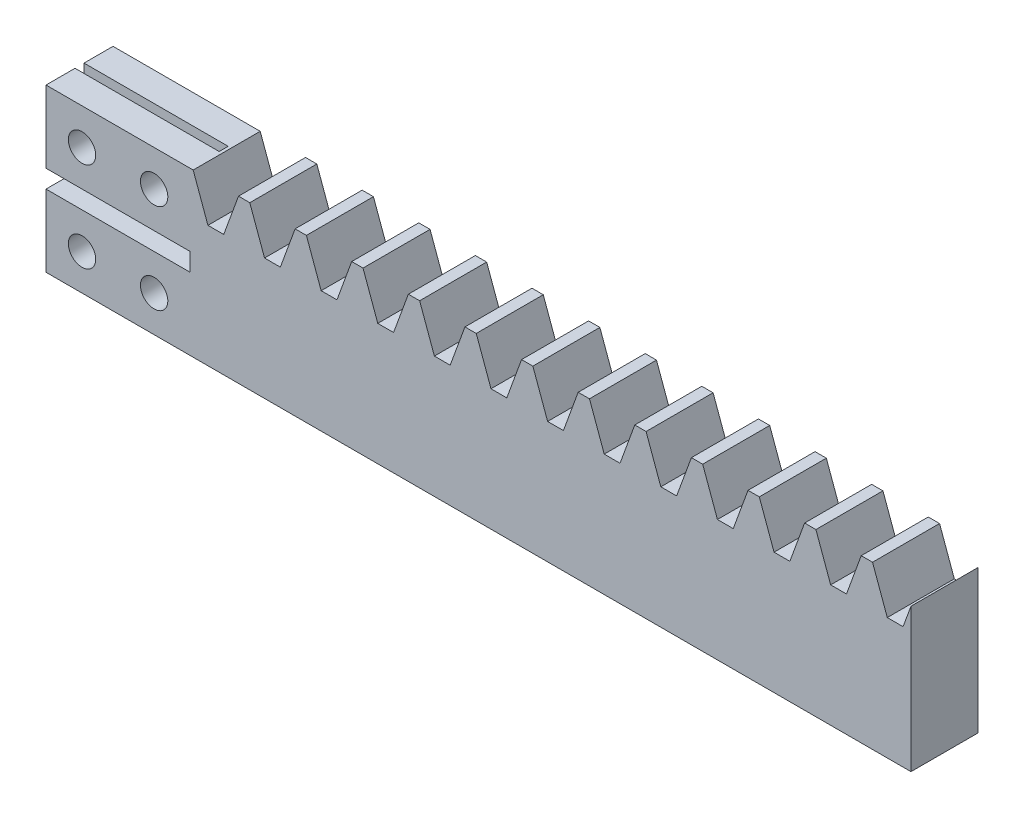
SolidWorks part; units mm, degrees
ref_plane "Plane1" through (0, 0, 0) normal (0, 0, 1) x (1, 0, 0)
ref_plane "Plane2" through (0, 0, 0) normal (0, 1, 0) x (1, 0, 0)
ref_plane "Plane3" through (0, 0, 0) normal (1, 0, 0) x (0, 0, -1)
sketch "HoldingSke" plane through (0, 0, 0) normal (0, 1, 0) x (1, 0, 0)
  line L0 (0, 0) -> (155.6602, -130.6144)
  line L1 (-15, 0) -> (100, 0) construction
  line L2 (0, 0) -> (-2.1039, 2.3779)
  line L3 (0, 0) -> (-11.863, 4.5341)
  line L4 (0, 0) -> (8.2587, 2.5249)
  line L5 (0, 0) -> (-23.7986, -8.8762)
  line L6 (0, 0) -> (-10.5278, -7.1032)
  line L9 (-71.009, 38.7566) -> (72.2002, 90.8805)
  line L10 (-76.2, 71.12) -> (-50.8, 71.12)
  line L11 (0, 0) -> (-11.811, 0)
  line L12 (-76.2, 101.6) -> (-76.0857, 101.6)
  line L13 (24.9733, 27.94) -> (52.9518, 28.4284)
  line L14 (24.9733, 27.94) -> (24.9746, 27.94)
  line L15 (24.9733, 27.94) -> (100.4006, 29.5858)
  circle A0 centre (0, 0) radius 19.05
  circle A1 centre (0, 0) radius 12.7
  circle A2 centre (0, 0) radius 12.7
  dimension "MPH" = 25.4
  dimension "Diameter" = 38.1
  dimension "Num_teeth" = 17
  dimension "Pitch" = 203.2
  dimension "Width" = 11.811
  dimension "Show_teeth" = 400
  dimension "Thickness" = 12.7
  dimension "Ap" = 20
  dimension "Pitch_height" = 25.4
  dimension "Backlash" = 0.1143
  dimension "Addendum_fac" = 1
  dimension "Dedendum_fac" = 1.25
  dimension "Clearance_fac" = 0.25
  dimension "Dedendum_add" = 0.0013
  dimension "Length" = 152.4
sketch "BlankSke" plane through (0, 0, 0) normal (0, 0, 1) x (1, 0, 0)
  line L1 (0, 0) -> (152.4, 0)
  line L2 (0, 0) -> (0, 28.575)
  line L3 (0, 28.575) -> (152.4, 28.575)
  line L4 (152.4, 0) -> (152.4, 28.575)
  dimension "Length" = 152.4
  dimension "Blank_height" = 28.575
extrude "Blank" add sketch "BlankSke" against normal blind 11.811
sketch "TooCutSkeIll" plane through (0, 0, 0) normal (0, 0, 1) x (1, 0, 0)
  line L0 (-3.9617, 28.4914) -> (-1.5824, 21.9544)
  line L1 (-0.8354, 21.4312) -> (0.8354, 21.4312)
  line L2 (1.5824, 21.9544) -> (3.9617, 28.4914)
  line L3 (152.4, 28.575) -> (0, 28.575) construction
  line L4 (0, 0) -> (0, 64.897) construction
  line L5 (-13.208, 25.4) -> (12.954, 25.4) construction
  line L6 (0, 0) -> (152.4, 0) construction
  line L7 (2.8365, 25.4) -> (2.8365, 48.7463) construction
  line L8 (-2.8365, 25.4) -> (-2.8365, 48.7463) construction
  line L9 (4.0811, 28.575) -> (4.0811, 28.6004)
  line L10 (-4.0811, 28.575) -> (-4.0811, 28.6004)
  line L11 (-4.0811, 28.6004) -> (4.0811, 28.6004)
  arc A0 (0.8354, 21.4312) -> (1.5824, 21.9544) centre (0.8354, 22.2263) ccw
  arc A1 (-1.5824, 21.9544) -> (-0.8354, 21.4312) centre (-0.8354, 22.2263) ccw
  arc A2 (4.0811, 28.575) -> (3.9617, 28.4914) centre (4.0811, 28.448) ccw
  arc A3 (-3.9617, 28.4914) -> (-4.0811, 28.575) centre (-4.0811, 28.448) ccw
  dimension "Root_fillet" = 0.795
  dimension "Break_rad" = 0.127
  dimension "Pitch_height" = 25.4
  dimension "Gap_width" = 5.6731
  dimension "Dedendum" = 3.9688
  dimension "Addendum_plus" = 3.2004
  dimension "Pressure_angle" = 20
extrude "ToothCutIll" [suppressed] cut sketch "TooCutSkeIll" against normal through all
sketch "TooCutSkeSim" plane through (0, 0, 0) normal (0, 0, 1) x (1, 0, 0)
  line L0 (1.392, 21.4312) -> (-1.392, 21.4312)
  line L1 (4.0014, 28.6004) -> (1.392, 21.4312)
  line L2 (0, 17.4625) -> (0, 53.467) construction
  line L3 (4.0014, 28.6004) -> (-4.0014, 28.6004)
  line L6 (-4.0014, 28.6004) -> (-1.392, 21.4312)
  line L9 (-2.8365, 25.4) -> (2.8365, 25.4) construction
  line L10 (0, 0) -> (152.4, 0) construction
  line L11 (2.8365, 25.4) -> (2.8365, 53.467) construction
  line L12 (-2.8365, 25.4) -> (-2.8365, 53.467) construction
  dimension "Pitch_height" = 25.4
  dimension "Pressure_angle" = 20
  dimension "Gap_width" = 5.6731
  dimension "Dedendum" = 3.9688
  dimension "Addendum_plus" = 3.2004
extrude "ToothCutSim" cut sketch "TooCutSkeSim" against normal through all
pattern_linear "TeethCuts" count 16 spacing 9.9746 along (1, 0, 0) of "ToothCutIll", "ToothCutSim"
sketch "Sketch2" plane through (0, 0, 0) normal (0, 0, 1) x (1, 0, 0)
  line L1 (0, 0) -> (23.9413, 0)
  line L2 (0, 0) -> (0, 28.575)
  line L3 (0, 28.575) -> (23.9413, 28.575)
  line L4 (23.9413, 0) -> (23.9413, 28.575)
extrude "Boss-Extrude1" add sketch "Sketch2" against normal blind 11.811
sketch "Sketch3" plane through (0, 0, 0) normal (0, 0, 1) x (1, 0, 0)
  line L0 (0, 12.7) -> (25.4, 12.7)
  line L1 (0, 28.575) -> (0, 0) construction
  line L2 (25.4, 12.7) -> (25.4, 15.875)
  line L3 (25.4, 15.875) -> (0, 15.875)
  line L4 (0, 14.2875) -> (13.4363, 14.2875) construction
  dimension "D1" = 25.4
  dimension "D2" = 3.175
  dimension "D3" = 3.175
extrude "Cut-Extrude1" cut sketch "Sketch3" against normal through all and the other way through all
sketch "Sketch4" plane through (0, 28.575, 0) normal (0, 1, 0) x (1, 0, 0)
  line L0 (0, 6.6993) -> (25.4, 6.6993)
  line L1 (0, 11.811) -> (0, 0) construction
  line L2 (25.4, 6.6993) -> (25.4, 5.1118)
  line L3 (25.4, 5.1118) -> (0, 5.1117)
  line L4 (0, 5.9055) -> (23.2466, 5.9055) construction
  dimension "D1" = 0.7937
  dimension "D2" = 0.7937
  dimension "D3" = 25.4
extrude "Cut-Extrude5" cut sketch "Sketch4" against normal through all and the other way through all flip side to cut
sketch "Sketch5" plane through (0, 0, 0) normal (0, 0, 1) x (1, 0, 0)
  line L0 (0, 28.575) -> (0, 15.875) construction
  line L1 (25.4, 15.875) -> (0, 15.875) construction
  line L2 (0, 12.7) -> (25.4, 12.7) construction
  circle A0 centre (6.35, 22.225) radius 2.413
  circle A1 centre (19.05, 22.225) radius 2.413
  circle A2 centre (19.05, 6.35) radius 2.413
  circle A3 centre (6.35, 6.35) radius 2.413
  dimension "D1" = 4.826
  dimension "D2" = 12.7
  dimension "D3" = 6.35
  dimension "D4" = 6.35
  dimension "D5" = 6.35
extrude "Cut-Extrude6" cut sketch "Sketch5" against normal blind 12.446
equation "' \"Pitch@HoldingSke\" = 4"
equation "' \"Num_teeth@HoldingSke\" = 12"
equation "' \"Ap@HoldingSke\" =  20"
equation "' \"Width@HoldingSke\" = 0.25"
equation "' \"Show_teeth@HoldingSke\" = 500"
equation "' \"Backlash@HoldingSke\" = 0.009"
equation "' \"Addendum_fac@HoldingSke\" = 1.0"
equation "' \"Dedendum_fac@HoldingSke\" = 1.25"
equation "' \"Dedendum_add@HoldingSke\" = 0.00005"
equation "' \"Clearance_fac@HoldingSke\" = 0.25"
equation "' \"Pitch_height@HoldingSke\" = 1"
equation "' \"Length@HoldingSke\" = 4.71"
equation "\"MPH@HoldingSke\" = \"Dedendum_fac@HoldingSke\" / \"Pitch@HoldingSke\" + 2 * \"Dedendum_add@HoldingSke\" + 0.002"
equation "\"MPH@HoldingSke\" = ((sgn( \"MPH@HoldingSke\" - \"Pitch_height@HoldingSke\")+1)*( \"MPH@HoldingSke\" - \"Pitch_height@HoldingSke\"))/2 + \"Pitch_height@HoldingSke\""
equation "\"Blank_height@BlankSke\" = \"Pitch_height@HoldingSke\" + \"Addendum_fac@HoldingSke\"  / \"Pitch@HoldingSke\" "
equation "\"Length@BlankSke\" =  \"Length@HoldingSke\""
equation "\"Face_width@Blank\" = \"Width@HoldingSke\""
equation "\"Pressure_angle@TooCutSkeIll\" = \"Ap@HoldingSke\""
equation "\"Addendum_plus@TooCutSkeIll\" =  \"Addendum_fac@HoldingSke\"  / \"Pitch@HoldingSke\" + 0.001"
equation "\"Dedendum@TooCutSkeIll\" = \"Dedendum_fac@HoldingSke\"  / \"Pitch@HoldingSke\""
equation "\"Pitch_height@TooCutSkeIll\" =  \"MPH@HoldingSke\""
equation "\"Gap_width@TooCutSkeIll\" = 3.14159265 / 2 / \"Pitch@HoldingSke\" + 6 * \"Backlash@HoldingSke\""
equation "\"Pressure_angle@TooCutSkeSim\" = \"Ap@HoldingSke\""
equation "\"Addendum_plus@TooCutSkeSim\" =  \"Addendum_fac@HoldingSke\"  / \"Pitch@HoldingSke\" + 0.001"
equation "\"Dedendum@TooCutSkeSim\" = \"Dedendum_fac@HoldingSke\"  / \"Pitch@HoldingSke\""
equation "\"Pitch_height@TooCutSkeSim\" =  \"MPH@HoldingSke\""
equation "\"Gap_width@TooCutSkeSim\" = 3.14159265 / 2 / \"Pitch@HoldingSke\" + 6 * \"Backlash@HoldingSke\""
equation "\"Root_fillet@TooCutSkeIll\" = \"Clearance_fac@HoldingSke\" / \"Pitch@HoldingSke\" + \"Dedendum_add@HoldingSke\""
equation "\"Break_rad@TooCutSkeIll\" = 0.02 / \"Pitch@HoldingSke\" * 2"
equation "\"Linear_pitch@TeethCuts\" = 3.14159265 / \"Pitch@HoldingSke\""
equation "\"Num_teeth@HoldingSke\" = int( ( \"Length@HoldingSke\" + 0 ) / (3.14159265 / \"Pitch@HoldingSke\")) + 0.9999  + 1"
equation " \"Num_teeth@TeethCuts\" = int( \"Show_teeth@HoldingSke\" ) + 1"
equation " \"Num_teeth@TeethCuts\" = ((sgn( \"Num_teeth@TeethCuts\" - \"Num_teeth@HoldingSke\" )-1)*( \"Num_teeth@TeethCuts\" - \"Num_teeth@HoldingSke\" ))/-2+ \"Num_teeth@HoldingSke\""
equation " \"Num_teeth@TeethCuts\" = ((sgn( \"Num_teeth@TeethCuts\" - 2.0)+1)*( \"Num_teeth@TeethCuts\" - 2.0))/2 +2.0"
